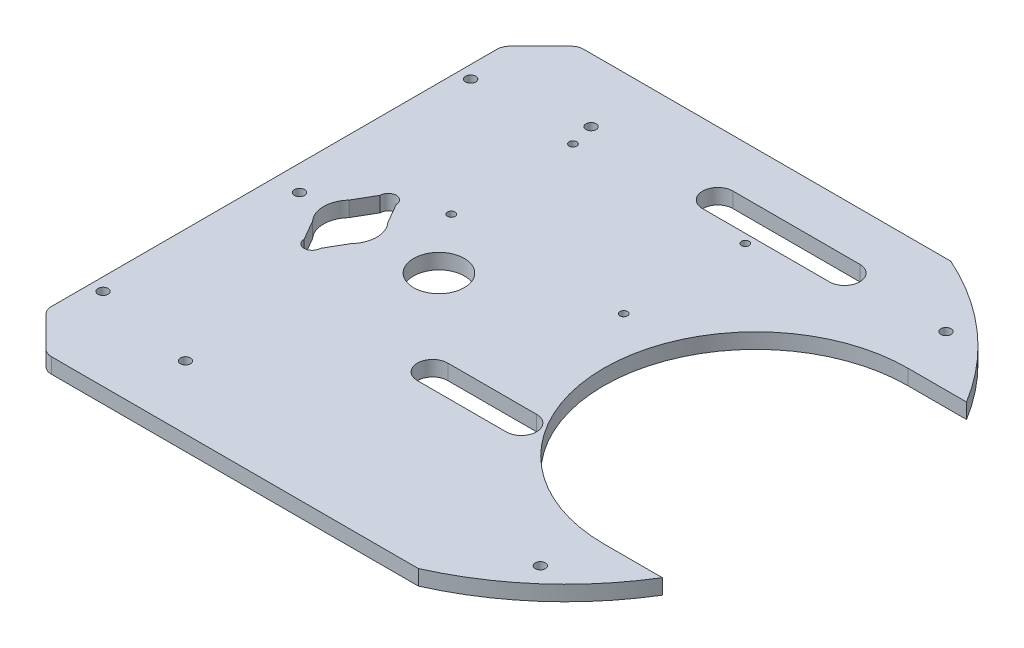
SolidWorks part; units mm, degrees
ref_plane "Front Plane" through (0, 0, 0) normal (0, 0, 1) x (1, 0, 0)
ref_plane "Top Plane" through (0, 0, 0) normal (0, 1, 0) x (1, 0, 0)
ref_plane "Right Plane" through (0, 0, 0) normal (1, 0, 0) x (0, 0, -1)
sketch "Sketch1" plane through (0, 0, 0) normal (0, 1, 0) x (1, 0, 0)
  line L1 (-46.9042, -105) -> (46.9042, -105)
  line L2 (-46.9042, 105) -> (46.9042, 105)
  line L7 (-70, 0) -> (70, 0) construction
  line L8 (-70, 80) -> (70, 80) construction
  line L9 (-70, 80) -> (-70, -80) construction
  line L10 (-70, -80) -> (70, -80) construction
  line L11 (70, 80) -> (70, -80) construction
  circle A0 centre (-70, 80) radius 2
  circle A1 centre (70, 80) radius 2
  circle A2 centre (70, -80) radius 2
  circle A3 centre (-70, -80) radius 2
  circle A4 centre (-85, 0) radius 10.5
  arc A8 (-46.9042, 105) -> (-46.9042, -105) centre (0, 0) ccw
  arc A9 (46.9042, -105) -> (46.9042, 105) centre (0, 0) ccw
  point P0 (0, 0)
  point P13 (0, 0)
  dimension "D1" = 105
  dimension "D8" = 230
  dimension "D5" = 4
  dimension "D6" = 21
  dimension "D2" = 140
  dimension "D3" = 160
  dimension "D4" = 105
  dimension "D7" = 85
  dimension "D9" = 105
extrude "Boss-Extrude1" add sketch "Sketch1" along normal blind 6
sketch "Sketch2" plane through (0, 0, 0) normal (0, -1, 0) x (1, 0, 0)
  line L0 (-95.5, 0) -> (-74.5, 0) construction
  line L1 (-85, 18.1537) -> (-85, -10.5) construction
  line L2 (-88.1537, 15) -> (-92.6802, 7.1599)
  line L3 (-81.8463, -15) -> (-77.3198, -7.1599)
  line L4 (-81.8463, 15) -> (-77.3198, 7.1599)
  line L5 (-88.1537, -15) -> (-92.6802, -7.1599)
  line L6 (-20, -80) -> (30, -80) construction
  line L7 (-20, -74) -> (30, -74)
  line L8 (-20, -86) -> (30, -86)
  line L9 (17.5, 35) -> (-17.5, 35) construction
  line L10 (17.5, 29) -> (-17.5, 29)
  line L11 (17.5, 41) -> (-17.5, 41)
  circle A0 centre (-85, 0) radius 10.5 construction
  arc A1 (-92.6802, 7.1599) -> (-92.6802, -7.1599) centre (-85, 0) ccw
  arc A2 (-81.8463, 15) -> (-88.1537, 15) centre (-85, 15) ccw
  arc A3 (-81.8463, -15) -> (-88.1537, -15) centre (-85, -15) cw
  arc A4 (-77.3198, -7.1599) -> (-77.3198, 7.1599) centre (-85, 0) ccw
  circle A5 centre (-50, 0) radius 10
  arc A6 (-20, -74) -> (-20, -86) centre (-20, -80) ccw
  arc A7 (30, -86) -> (30, -74) centre (30, -80) ccw
  arc A8 (17.5, 29) -> (17.5, 41) centre (17.5, 35) ccw
  arc A9 (-17.5, 41) -> (-17.5, 29) centre (-17.5, 35) ccw
  circle A10 centre (-105, 0) radius 2
  arc A11 (-46.9042, 105) -> (-46.9042, -105) centre (0, 0) ccw construction
  point P20 (5, -80)
  point P28 (0, 35)
  point P35 (-115, 0)
  dimension "D2" = 6.3075
  dimension "D3" = 30
  dimension "D5" = 20
  dimension "D8" = 6
  dimension "D11" = 6
  dimension "D15" = 4
  dimension "D1" = 15
  dimension "D4" = 30
  dimension "D6" = 35
  dimension "D7" = 50
  dimension "D9" = 80
  dimension "D10" = 90
  dimension "D12" = 35
  dimension "D13" = 35
  dimension "D14" = 10
extrude "Cut-Extrude2" cut sketch "Sketch2" against normal blind 19
ref_plane "Plane1" through (0, 0, 0) normal (0, -1, 0) x (-1, 0, 0)
sketch "Sketch3" plane through (0, 0, 0) normal (0, -1, 0) x (-1, 0, 0)
  line L0 (46.9042, -105) -> (115, -105)
  line L1 (46.9042, 105) -> (115, 105)
  line L2 (115, 105) -> (115, -105)
  arc A1 (46.9042, -105) -> (46.9042, 105) centre (0, 0) ccw construction
  arc A2 (46.9042, -105) -> (46.9042, 105) centre (0, 0) ccw
  dimension "D1" = 68.0958
extrude "Boss-Extrude2" add sketch "Sketch3" against normal blind 6 contours A2 L0 L2 | A2 L2 L1
chamfer "Chamfer1" distance 15 angle 45 2 edges at (-115, 3, -105) (-115, 3, 105)
fillet "Fillet1" radius 5 4 edges at (-100, 3, -105) (-115, 3, -90) (-100, 3, 105) (-115, 3, 90)
sketch "Sketch4" plane through (0, 6, 0) normal (0, 1, 0) x (1, 0, 0)
  line L0 (115, -60) -> (75, -60)
  line L1 (115, 60) -> (75, 60)
  line L2 (75, 0) -> (213.8113, 0) construction
  line L3 (115, -60) -> (115, 60)
  line L4 (30, 86) -> (-20, 86) construction
  line L5 (-97.9289, -105) -> (46.9042, -105) construction
  arc A0 (75, 60) -> (75, -60) centre (75, 0) ccw
  circle A1 centre (0.3198, 22.5362) radius 1.5
  circle A2 centre (-67.6802, 22.5362) radius 1.5
  circle A3 centre (-67.6802, 70.5362) radius 1.5
  circle A4 centre (0.3198, 70.5362) radius 1.5
  dimension "D4" = 40
  dimension "D3" = 15
  dimension "D6" = 3
  dimension "D1" = 60
  dimension "D2" = 60
  dimension "D5" = 105
  dimension "D9" = 25
  dimension "D10" = 68
  dimension "D11" = 122.6802
  dimension "D12" = 15.4638
  dimension "D13" = 63.4638
  dimension "D7" = 2
  dimension "D8" = 2
extrude "Cut-Extrude3" cut sketch "Sketch4" against normal blind 10
sketch "Sketch5" plane through (0, 6, 0) normal (0, 1, 0) x (1, 0, 0)
  line L0 (0, 0) -> (-139.8206, 0) construction
  line L1 (-115, 87.9289) -> (-115, -87.9289) construction
  circle A0 centre (-110, -72.5) radius 2
  circle A1 centre (-110, 72.5) radius 2
  point P7 (0, 0)
  dimension "D1" = 4
  dimension "D2" = 4
  dimension "D3" = 5
  dimension "D4" = 72.5
  dimension "D5" = 72.5
extrude "Cut-Extrude4" cut sketch "Sketch5" against normal blind 10
